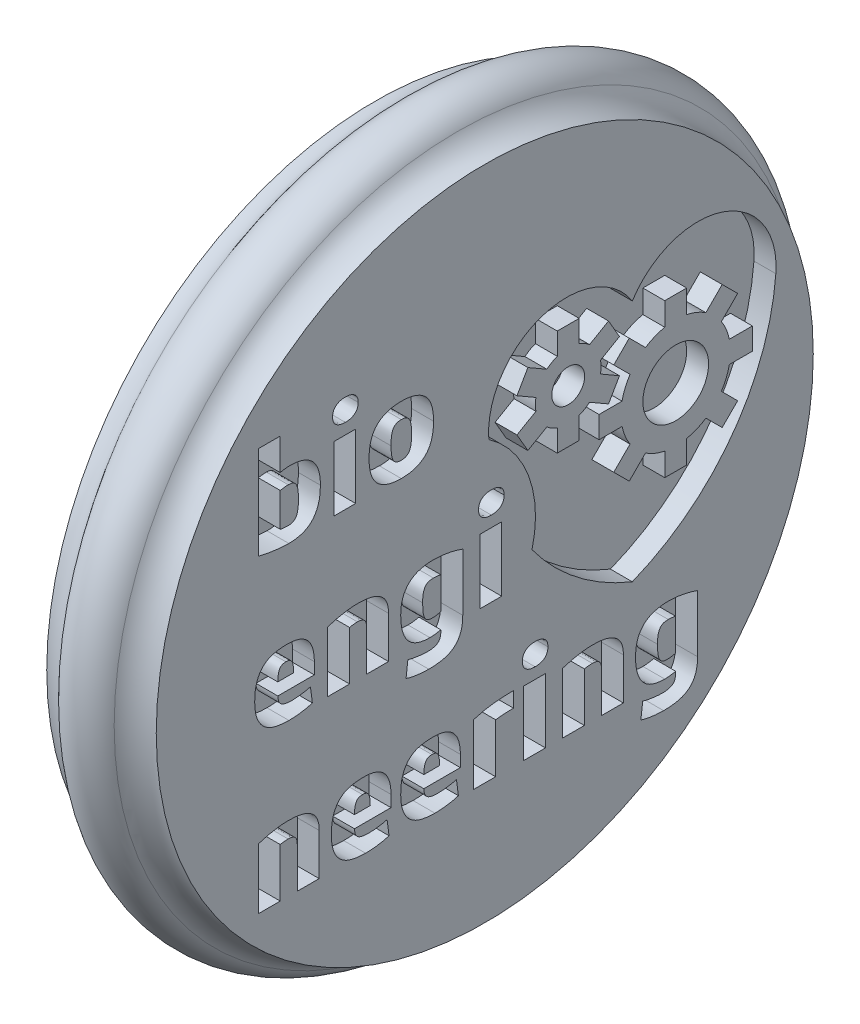
SolidWorks part; units mm, degrees
ref_plane "Alzado" through (0, 0, 0) normal (0, 0, 1) x (1, 0, 0)
ref_plane "Planta" through (0, 0, 0) normal (0, 1, 0) x (1, 0, 0)
ref_plane "Vista lateral" through (0, 0, 0) normal (1, 0, 0) x (0, 0, -1)
sketch "Sketch3" plane through (0, 0, 0) normal (0, 0, 1) x (1, 0, 0)
  line L0 (0, 0) -> (0, 16.7873) construction
  line L1 (2.5, 0) -> (2.5, 15)
  line L2 (-2.5, 0) -> (-2.5, 15)
  line L3 (-2.5, 0) -> (2.5, 0)
  arc A0 (1.25, 15.6708) -> (-1.25, 15.6708) centre (0, 14.8417) ccw
  arc A1 (1.25, 15.6708) -> (2.5, 15) centre (2.5, 16.5) ccw
  arc A2 (-1.25, 15.6708) -> (-2.5, 15) centre (-2.5, 16.5) cw
  dimension "D1" = 3
  dimension "D4" = 3
  dimension "D2" = 15
  dimension "D3" = 2.5
revolve "Revolve1" add sketch "Sketch3" angle 360 about L3
sketch "Sketch4" plane through (-2.5, 0, 0) normal (-1, 0, 0) x (0, 0, 1)
  line L1 (74.3509, 235.2726) -> (407.6843, 235.2726) construction
  line L2 (-10.6534, 2.7336) -> (-9.5782, 1.7539)
  line L3 (-10.6534, 8.0639) -> (-9.5782, 8.0639)
  line L4 (-10.6534, 8.0639) -> (-10.6534, 2.7336)
  line L5 (-9.5782, 1.7539) -> (-4.7756, 1.7539)
  line L6 (-4.7756, 8.0639) -> (-4.7756, 1.7539)
  line L8 (-9.5782, 8.0639) -> (-9.5782, 2.733)
  line L9 (-9.5782, 2.733) -> (-5.8508, 2.733)
  line L10 (-5.8508, 8.0639) -> (-5.8508, 2.733)
  line L11 (-5.8508, 8.0639) -> (-4.7756, 8.0639)
  line L12 (-2.9239, 2.7109) -> (-1.8736, 1.7539)
  line L13 (-2.9239, 9.5707) -> (-1.825, 9.5707)
  line L14 (-2.9239, 9.5707) -> (-2.9239, 11.0136)
  line L15 (-2.9239, 11.0136) -> (-1.825, 11.0136)
  line L16 (-1.825, 9.5707) -> (-1.825, 11.0136)
  line L17 (-2.9239, 8.0639) -> (-1.825, 8.0639)
  line L18 (-2.9239, 8.0639) -> (-2.9239, 2.7109)
  line L19 (-1.8736, 1.7539) -> (2.7209, 1.7539)
  line L20 (2.7209, 2.733) -> (2.7209, 1.7539)
  line L21 (-1.825, 8.0639) -> (-1.825, 2.733)
  line L22 (-1.825, 2.733) -> (2.7209, 2.733)
  line L25 (5.2465, 8.0639) -> (4.1977, 7.096)
  line L26 (10.0535, 1.7539) -> (5.2465, 1.7539)
  line L27 (10.0535, 1.7539) -> (10.0535, 2.733)
  line L28 (10.0535, 8.0639) -> (5.2465, 8.0639)
  line L29 (4.1977, 2.733) -> (4.1977, 7.096)
  line L30 (10.0535, 2.733) -> (5.2465, 2.733)
  line L32 (10.0535, 7.096) -> (5.2465, 7.096)
  line L33 (5.2465, 2.733) -> (5.2465, 7.096)
  line L34 (5.2465, 1.7539) -> (4.1977, 2.733)
  line L35 (10.0535, 7.096) -> (10.0535, 8.0639)
  line L36 (-2.0904, -2.8633) -> (-3.1392, -3.8312)
  line L37 (2.7165, -9.1733) -> (-2.0904, -9.1733)
  line L38 (2.7165, -9.1733) -> (2.7165, -8.1942)
  line L39 (2.7165, -2.8633) -> (-2.0904, -2.8633)
  line L40 (-3.1392, -8.1942) -> (-3.1392, -3.8312)
  line L41 (2.7165, -8.1942) -> (-2.0904, -8.1942)
  line L42 (2.7165, -3.8312) -> (-2.0904, -3.8312)
  line L43 (-2.0904, -8.1942) -> (-2.0904, -3.8312)
  line L44 (-2.0904, -9.1733) -> (-3.1392, -8.1942)
  line L45 (2.7165, -3.8312) -> (2.7165, -2.8633)
  line L46 (-10.6534, 0.0588) -> (-10.6534, -8.1942)
  line L47 (-10.6534, 0.0588) -> (-9.5782, 0.0588)
  line L48 (-9.5782, 0.0588) -> (-9.5782, -2.8633)
  line L49 (-9.5782, -2.8633) -> (-5.8508, -2.8633)
  line L50 (-5.8508, -2.8633) -> (-4.7756, -3.867)
  line L51 (-4.7756, -3.867) -> (-4.7756, -8.1942)
  line L52 (-4.7756, -8.1942) -> (-5.8508, -9.1865)
  line L53 (-5.8508, -9.1865) -> (-9.5782, -9.1865)
  line L54 (-9.5782, -9.1865) -> (-10.6534, -8.1942)
  line L55 (4.1977, -9.1733) -> (4.1977, -2.86)
  line L56 (-9.5782, -3.867) -> (-5.8508, -3.867)
  line L57 (-9.5782, -3.867) -> (-9.5782, -8.1942)
  line L58 (-9.5782, -8.1942) -> (-5.8508, -8.1942)
  line L59 (-5.8508, -3.867) -> (-5.8508, -8.1942)
  line L60 (4.1977, -2.86) -> (8.9432, -2.86)
  line L61 (8.9432, -2.86) -> (10.0535, -3.8887)
  line L62 (10.0535, -3.8887) -> (10.0535, -9.1733)
  line L63 (10.0535, -9.1733) -> (8.9432, -9.1733)
  line L64 (8.9432, -9.1733) -> (8.9432, -3.8347)
  line L65 (8.9432, -3.8347) -> (5.2465, -3.8347)
  line L66 (5.2465, -3.8347) -> (5.2465, -9.1733)
  line L67 (5.2465, -9.1733) -> (4.1977, -9.1733)
extrude "Cut-Extrude1" cut sketch "Sketch4" against normal blind 1
sketch "Sketch5" plane through (2.5, 0, 0) normal (1, 0, 0) x (0, 0, -1)
  line L0 (-10.7265, 4.5333) -> (11.5591, 4.5333) construction
  text T0 "<b>bio</b>\r\n<b>engi</b>\r\n<b>neering</b>" font "3ds" height 4
extrude "Cut-Extrude2" cut sketch "Sketch5" against normal blind 1
sketch "Sketch10" plane through (2.5, 0, 0) normal (1, 0, 0) x (0, 0, -1)
  line L0 (35.0041, 138.7381) -> (263.6708, 138.7381) construction
  line L1 (24.5522, 94.7869) -> (146.5522, 94.7869) construction
  line L2 (123.4623, 351.1969) -> (623.4623, 351.1969) construction
  line L3 (6.7376, -4.9095) -> (6.7376, 6.247) construction
  arc A0 (6.7376, 6.2262) -> (0.1842, 4.0273) centre (3.737, 4.3036) ccw
  arc A1 (0.1842, 4.0273) -> (6.7376, -4.8776) centre (10.6129, 4.8383) ccw
  arc A2 (13.291, 4.0273) -> (6.7376, -4.8776) centre (2.8623, 4.8383) cw
  arc A3 (6.7376, 6.2262) -> (13.291, 4.0273) centre (9.7381, 4.3036) cw
  arc A4 (2.1576, -1.32) -> (0.1842, 4.0273) centre (-2.6833, -0.0687) ccw
  dimension "D1" = 5
extrude "Cut-Extrude3" cut sketch "Sketch10" against normal blind 1 contours A4 A1 A2 A3 A0
sketch "Sketch12" plane through (1.5, 0, 0) normal (1, 0, 0) x (0, 0, -1)
  line L0 (8.7191, 1.9972) -> (8.7191, 5.8881) construction
  line L2 (8.2191, 4.4467) -> (8.2191, 5.4972)
  line L3 (8.2191, 5.4972) -> (9.2191, 5.4972)
  line L4 (9.2191, 4.4467) -> (9.2191, 5.4972)
  line L5 (10.0976, 4.0828) -> (10.8404, 4.8256)
  line L6 (10.8404, 4.8256) -> (11.5476, 4.1185)
  line L7 (10.8047, 3.3757) -> (11.5476, 4.1185)
  line L8 (11.1686, 2.4972) -> (12.2191, 2.4972)
  line L9 (12.2191, 2.4972) -> (12.2191, 1.4972)
  line L10 (11.1686, 1.4972) -> (12.2191, 1.4972)
  line L11 (10.8047, 0.6187) -> (11.5476, -0.1241)
  line L12 (11.5476, -0.1241) -> (10.8404, -0.8312)
  line L13 (10.0976, -0.0884) -> (10.8404, -0.8312)
  line L14 (9.2191, -0.4523) -> (9.2191, -1.5028)
  line L15 (9.2191, -1.5028) -> (8.2191, -1.5028)
  line L16 (8.2191, -0.4523) -> (8.2191, -1.5028)
  line L17 (7.3406, -0.0884) -> (6.5978, -0.8312)
  line L18 (6.5978, -0.8312) -> (5.8907, -0.1241)
  line L19 (6.6335, 0.6187) -> (5.8907, -0.1241)
  line L20 (6.2696, 1.4972) -> (5.2191, 1.4972)
  line L21 (5.2191, 1.4972) -> (5.2191, 2.4972)
  line L22 (6.2696, 2.4972) -> (5.2191, 2.4972)
  line L23 (6.6335, 3.3757) -> (5.8907, 4.1185)
  line L24 (5.8907, 4.1185) -> (6.5978, 4.8256)
  line L25 (7.3406, 4.0828) -> (6.5978, 4.8256)
  line L26 (3.8108, 4.3364) -> (3.8108, 6.8595) construction
  line L28 (3.3108, 5.7506) -> (3.3108, 6.7506)
  line L29 (3.3108, 6.7506) -> (4.3108, 6.7506)
  line L30 (4.3108, 5.7506) -> (4.3108, 6.7506)
  line L31 (4.7856, 5.4765) -> (5.6516, 5.9765)
  line L32 (5.6516, 5.9765) -> (6.1516, 5.1105)
  line L33 (5.2856, 4.6105) -> (6.1516, 5.1105)
  line L34 (5.2856, 4.0623) -> (6.1516, 3.5623)
  line L35 (6.1516, 3.5623) -> (5.6516, 2.6962)
  line L36 (4.7856, 3.1962) -> (5.6516, 2.6962)
  line L37 (4.3108, 2.9222) -> (4.3108, 1.9222)
  line L38 (4.3108, 1.9222) -> (3.3108, 1.9222)
  line L39 (3.3108, 2.9222) -> (3.3108, 1.9222)
  line L40 (2.8361, 3.1962) -> (1.97, 2.6962)
  line L41 (1.97, 2.6962) -> (1.47, 3.5623)
  line L42 (2.3361, 4.0623) -> (1.47, 3.5623)
  line L43 (2.3361, 4.6105) -> (1.47, 5.1105)
  line L44 (1.47, 5.1105) -> (1.97, 5.9765)
  line L45 (2.8361, 5.4765) -> (1.97, 5.9765)
  circle A0 centre (8.7191, 1.9972) radius 1.5
  arc A1 (6.6335, 3.3757) -> (6.2696, 2.4972) centre (8.7191, 1.9972) ccw
  arc A2 (8.2191, 4.4467) -> (7.3406, 4.0828) centre (8.7191, 1.9972) ccw
  arc A3 (10.0976, 4.0828) -> (9.2191, 4.4467) centre (8.7191, 1.9972) ccw
  arc A4 (11.1686, 2.4972) -> (10.8047, 3.3757) centre (8.7191, 1.9972) ccw
  arc A5 (10.8047, 0.6187) -> (11.1686, 1.4972) centre (8.7191, 1.9972) ccw
  arc A6 (9.2191, -0.4523) -> (10.0976, -0.0884) centre (8.7191, 1.9972) ccw
  arc A7 (7.3406, -0.0884) -> (8.2191, -0.4523) centre (8.7191, 1.9972) ccw
  arc A8 (6.2696, 1.4972) -> (6.6335, 0.6187) centre (8.7191, 1.9972) ccw
  circle A9 centre (3.8108, 4.3364) radius 0.75
  arc A10 (3.3108, 5.7506) -> (2.8361, 5.4765) centre (3.8108, 4.3364) ccw
  arc A11 (4.7856, 5.4765) -> (4.3108, 5.7506) centre (3.8108, 4.3364) ccw
  arc A12 (5.2856, 4.0623) -> (5.2856, 4.6105) centre (3.8108, 4.3364) ccw
  arc A13 (4.3108, 2.9222) -> (4.7856, 3.1962) centre (3.8108, 4.3364) ccw
  arc A14 (2.8361, 3.1962) -> (3.3108, 2.9222) centre (3.8108, 4.3364) ccw
  arc A15 (2.3361, 4.6105) -> (2.3361, 4.0623) centre (3.8108, 4.3364) ccw
  point P38 (8.7191, 1.9972)
  point P63 (3.8108, 4.3364)
  dimension "D1" = 3
  dimension "D2" = 5
  dimension "D7" = 1.5
  dimension "D8" = 3
  dimension "D3" = 3.5
  dimension "D4" = 1
  dimension "D5" = 0.5
  dimension "D9" = 1
  dimension "D10" = 1
  dimension "D11" = 1
  dimension "D6" = 8
  dimension "D12" = 6
extrude "Boss-Extrude6" add sketch "Sketch12" along normal blind 1 contours L43 A15 L42 L41 L40 A14 L39 L38 L37 A13 L36 L35 L34 A12 L33 L32 L31 A11 L30 L29 L28 A10 L45 L44 A9 | L20 A8 L19 L18 L17 A7 L16 L15 L14 A6 L13 L12 L11 A5 L10 L9 L8 A4 L7 L6 L5 A3 L4 L3 L2 A2 L25 L24 L23 A1 L22 L21 A0
